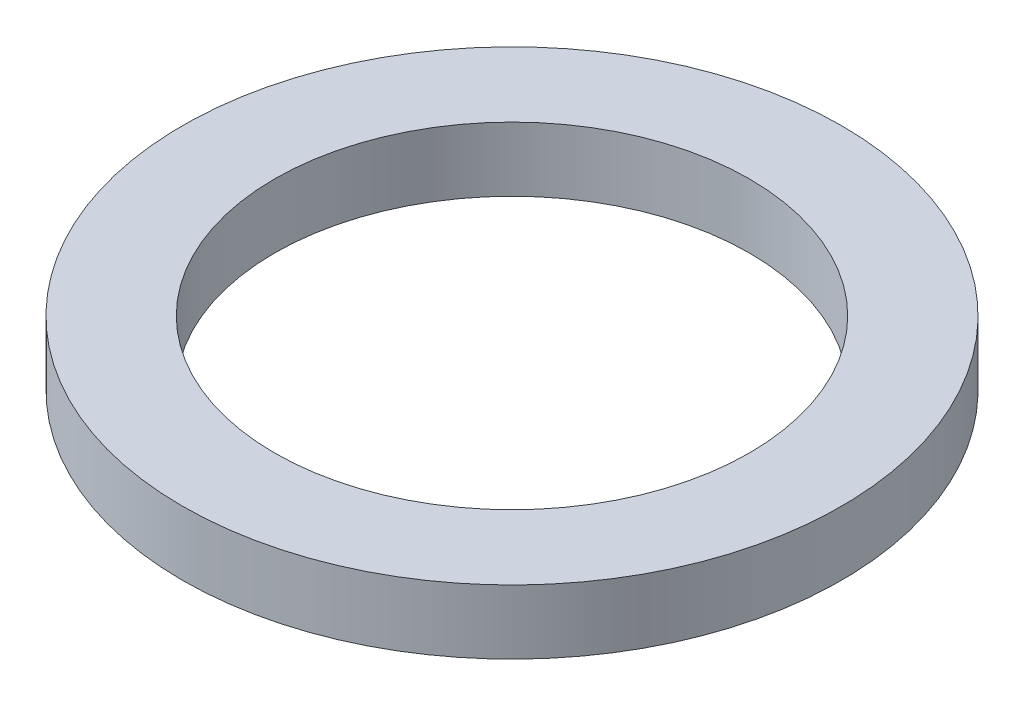
SolidWorks part; units mm, degrees
material "AISI 304"
ref_plane "Front Plane" through (0, 0, 0) normal (0, 0, 1) x (1, 0, 0)
ref_plane "Top Plane" through (0, 0, 0) normal (0, 1, 0) x (1, 0, 0)
ref_plane "Right Plane" through (0, 0, 0) normal (1, 0, 0) x (0, 0, -1)
sketch "Sketch1" plane through (0, 0, 0) normal (0, 1, 0) x (1, 0, 0)
  circle A0 centre (0, 0) radius 5.9
  circle A1 centre (0, 0) radius 4.25
  dimension "D1" = 8.5
  dimension "D2" = 11.8
extrude "Boss-Extrude1" add sketch "Sketch1" along normal blind 1.15
move or copy body "Sólido-Mover/Copiar1" [suppressed] bodies to move or copy 101
